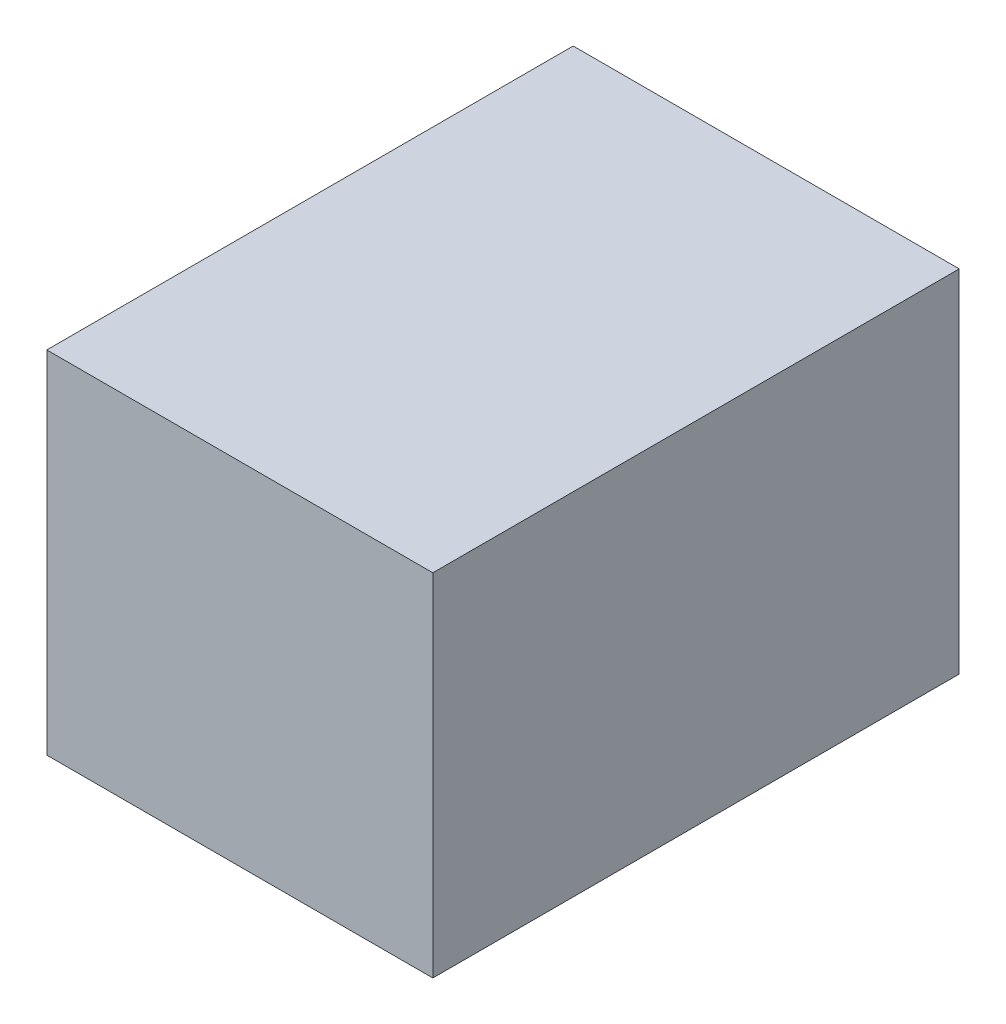
SolidWorks part; units mm, degrees
ref_plane "Front Plane" through (0, 0, 0) normal (0, 0, 1) x (1, 0, 0)
ref_plane "Top Plane" through (0, 0, 0) normal (0, 1, 0) x (1, 0, 0)
ref_plane "Right Plane" through (0, 0, 0) normal (1, 0, 0) x (0, 0, -1)
sketch "Sketch1" plane through (0, 0, 0) normal (0, 1, 0) x (1, 0, 0)
  line L1 (4.2846, -6.6638) -> (15.2846, -6.6638)
  line L2 (4.2846, -6.6638) -> (4.2846, -21.6638)
  line L3 (4.2846, -21.6638) -> (15.2846, -21.6638)
  line L4 (15.2846, -6.6638) -> (15.2846, -21.6638)
  line L5 (4.2846, -6.6638) -> (15.2846, -21.6638) construction
  line L6 (4.2846, -21.6638) -> (15.2846, -6.6638) construction
  point P0 (9.7846, -14.1638)
  dimension "D1" = 11
  dimension "D2" = 15
extrude "Boss-Extrude1" add sketch "Sketch1" along normal blind 10
